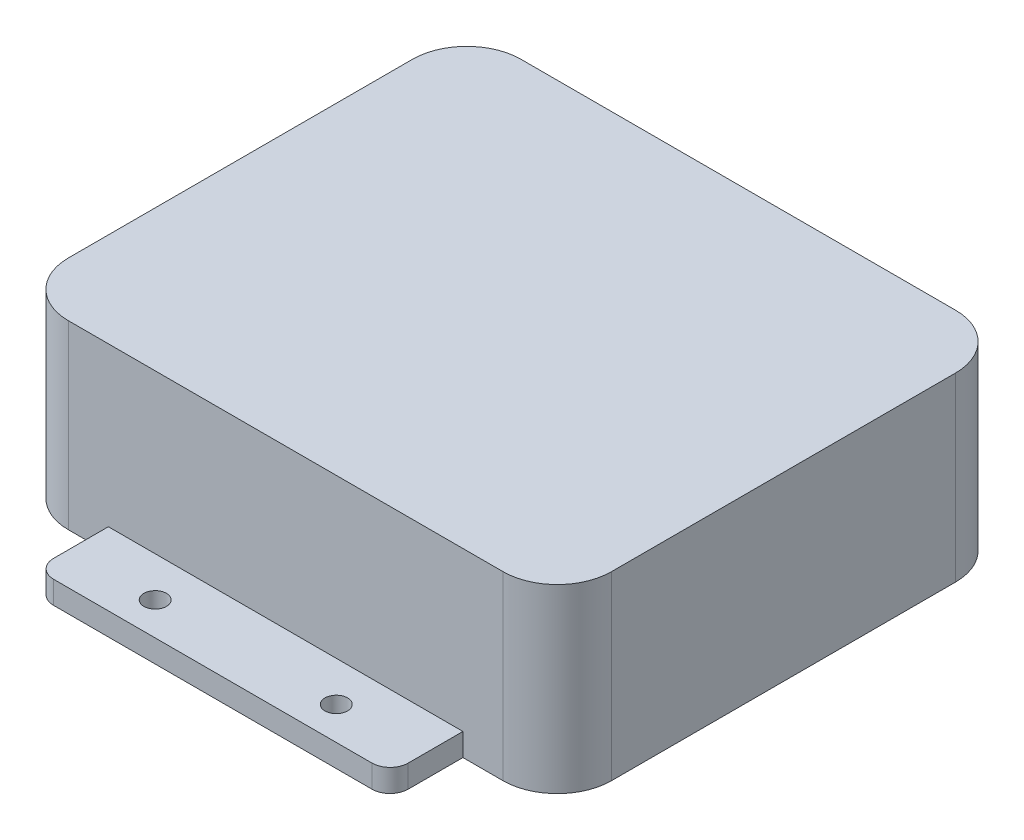
SolidWorks part; units mm, degrees
ref_plane "Front Plane" through (0, 0, 0) normal (0, 0, 1) x (1, 0, 0)
ref_plane "Top Plane" through (0, 0, 0) normal (0, 1, 0) x (1, 0, 0)
ref_plane "Right Plane" through (0, 0, 0) normal (1, 0, 0) x (0, 0, -1)
sketch "Sketch1" plane through (0, 0, 0) normal (0, 1, 0) x (1, 0, 0)
  line L1 (-30.48, -31.75) -> (30.48, -31.75)
  line L2 (-38.1, -24.13) -> (-38.1, 24.13)
  line L3 (-30.48, 31.75) -> (30.48, 31.75)
  line L4 (38.1, -24.13) -> (38.1, 24.13)
  line L5 (-38.1, -31.75) -> (38.1, 31.75) construction
  line L6 (-38.1, 31.75) -> (38.1, -31.75) construction
  arc A0 (-38.1, 24.13) -> (-30.48, 31.75) centre (-30.48, 24.13) cw
  arc A1 (-30.48, -31.75) -> (-38.1, -24.13) centre (-30.48, -24.13) cw
  arc A2 (30.48, -31.75) -> (38.1, -24.13) centre (30.48, -24.13) ccw
  arc A3 (30.48, 31.75) -> (38.1, 24.13) centre (30.48, 24.13) cw
  point P0 (0, 0)
  dimension "D3" = 7.62
  dimension "D4" = 7.62
  dimension "D1" = 63.5
  dimension "D2" = 76.2
extrude "Boss-Extrude1" add sketch "Sketch1" along normal blind 25.4 contours A3 L3 A0 L2 A1 L1 A2 L4
sketch "Sketch2" plane through (0, 0, 0) normal (0, 1, 0) x (1, 0, 0)
  line L0 (-13.97, 0) -> (13.97, 0) construction
  line L1 (0, -13.97) -> (0, 13.97) construction
  line L2 (-24.8695, -31.75) -> (24.8695, -31.75)
  line L4 (-22.3295, -41.9712) -> (22.3295, -41.9712)
  line L5 (24.8695, -31.75) -> (24.8695, -39.4312)
  line L6 (-24.8695, -31.75) -> (-24.8695, -39.4312)
  line L7 (-24.8695, 31.75) -> (-24.8695, 39.4312)
  line L8 (-22.3295, 41.9712) -> (22.3295, 41.9712)
  line L9 (24.8695, 31.75) -> (24.8695, 39.4312)
  line L10 (-24.8695, 31.75) -> (24.8695, 31.75)
  circle A0 centre (12.7, -37.35) radius 1.5875
  circle A1 centre (-12.7, -37.35) radius 1.5875
  arc A2 (24.8695, -39.4312) -> (22.3295, -41.9712) centre (22.3295, -39.4312) cw
  arc A3 (-22.3295, -41.9712) -> (-24.8695, -39.4312) centre (-22.3295, -39.4312) cw
  circle A4 centre (12.7, 37.35) radius 1.5875
  circle A5 centre (-12.7, 37.35) radius 1.5875
  arc A6 (-22.3295, 41.9712) -> (-24.8695, 39.4312) centre (-22.3295, 39.4312) ccw
  arc A7 (24.8695, 39.4312) -> (22.3295, 41.9712) centre (22.3295, 39.4312) ccw
  point P11 (24.8695, -41.9712)
  point P16 (-24.8695, -41.9712)
  dimension "D3" = 3.175
  dimension "D4" = 2.54
  dimension "D1" = 37.35
  dimension "D2" = 12.7
extrude "Boss-Extrude2" add sketch "Sketch2" along normal blind 3.175
